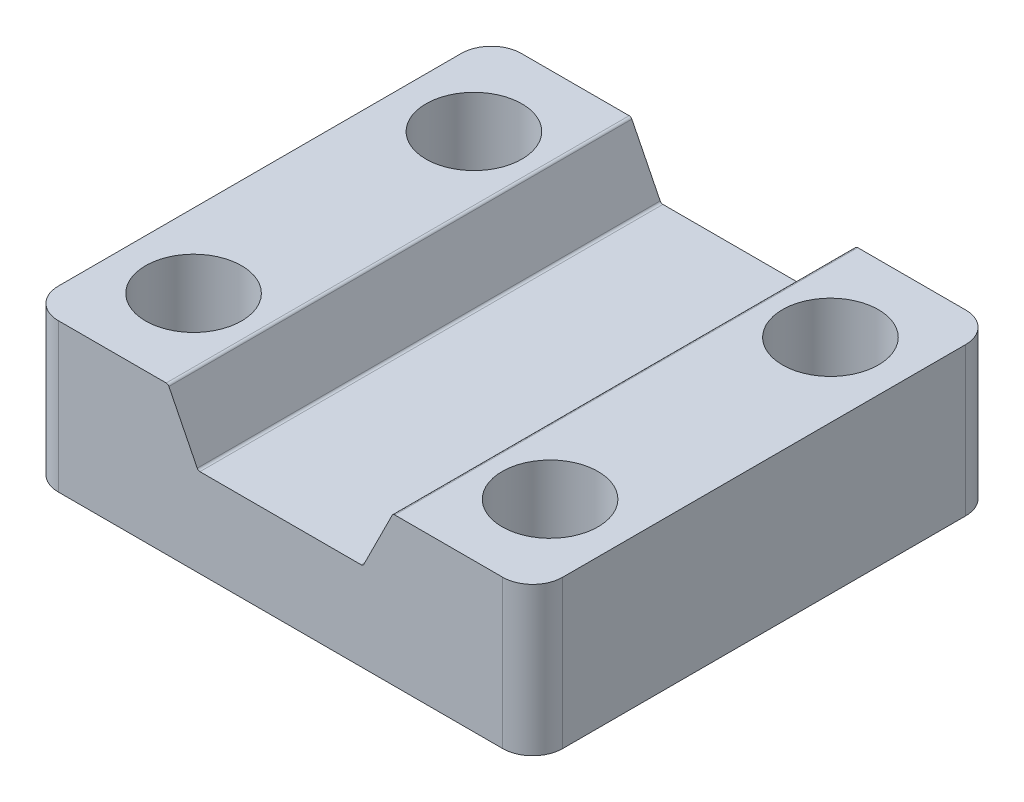
SolidWorks part; units mm, degrees
ref_plane "Plan de face" through (0, 0, 0) normal (0, 0, 1) x (1, 0, 0)
ref_plane "Plan de dessus" through (0, 0, 0) normal (0, 1, 0) x (1, 0, 0)
ref_plane "Plan de droite" through (0, 0, 0) normal (1, 0, 0) x (0, 0, -1)
ref_plane "Plan1" through (0, 12.573, 0) normal (0, 1, 0) x (1, 0, 0)
sketch "Esquisse1" plane through (0, 12.573, 0) normal (0, 1, 0) x (1, 0, 0)
  line L0 (-21.3614, 19.6088) -> (-21.3614, -19.6088)
  line L1 (-21.3614, -19.6088) -> (21.3614, -19.6088)
  line L2 (21.3614, -19.6088) -> (21.3614, 19.6088)
  line L3 (21.3614, 19.6088) -> (-21.3614, 19.6088)
extrude "Boss.-Extru.1" add sketch "Esquisse1" against normal blind 12.573
sketch "Esquisse2" plane through (0, 0, -19.6088) normal (0, 0, -1) x (-1, 0, 0)
  line L0 (-6.985, 12.573) -> (-6.985, 7.493)
  line L1 (-6.985, 7.493) -> (6.985, 7.493)
  line L2 (6.985, 7.493) -> (6.985, 12.573)
  line L3 (6.985, 12.573) -> (-6.985, 12.573)
extrude "Enlèv. mat.-Extru.1" cut sketch "Esquisse2" against normal through all
draft "Dépouille1" type of draft neutral plane draft angle 26.565 faces to draft 2 face at (-6.985, 10.033, 0) face at (6.985, 10.033, 0) neutral plane through (6.985, 7.493, 19.6088) neutral plane normal (0, 1, 0) parameters "D1"=26.565
hole_wizard "Perçage1" positions "Esquisse4" profile "Esquisse3" legacy
sketch "Esquisse4" plane through (0, 12.573, 0) normal (0, 1, 0) x (1, 0, 0)
  point P0 (15.1003, -11.8745)
  point P1 (-15.1003, 11.8745)
  point P2 (15.1003, 11.8745)
  point P3 (-15.1003, -11.8745)
sketch "Esquisse3" plane through (15.1003, 12.573, 11.8745) normal (1, 0, 0) x (0, 0, 1)
  line L0 (0, 0) -> (0, 12.573)
  line L1 (0, 12.573) -> (4.064, 12.573)
  line L2 (4.064, 12.573) -> (4.064, 0)
  line L3 (4.064, 0) -> (0, 0)
  line L4 (0, 110) -> (0, -10) construction
  dimension "Diamètre" = 8.128
  dimension "Profondeur" = 12.573
fillet "Congé1" radius 0.254 4 edges at (-6.985, 7.493, 0) (9.525, 12.573, 0) (6.985, 7.493, 0) (-9.525, 12.573, 0)
fillet "Congé2" radius 2.54 4 edges at (-21.3614, 6.2865, -19.6088) (21.3614, 6.2865, -19.6088) (-21.3614, 6.2865, 19.6088) (21.3614, 6.2865, 19.6088)
